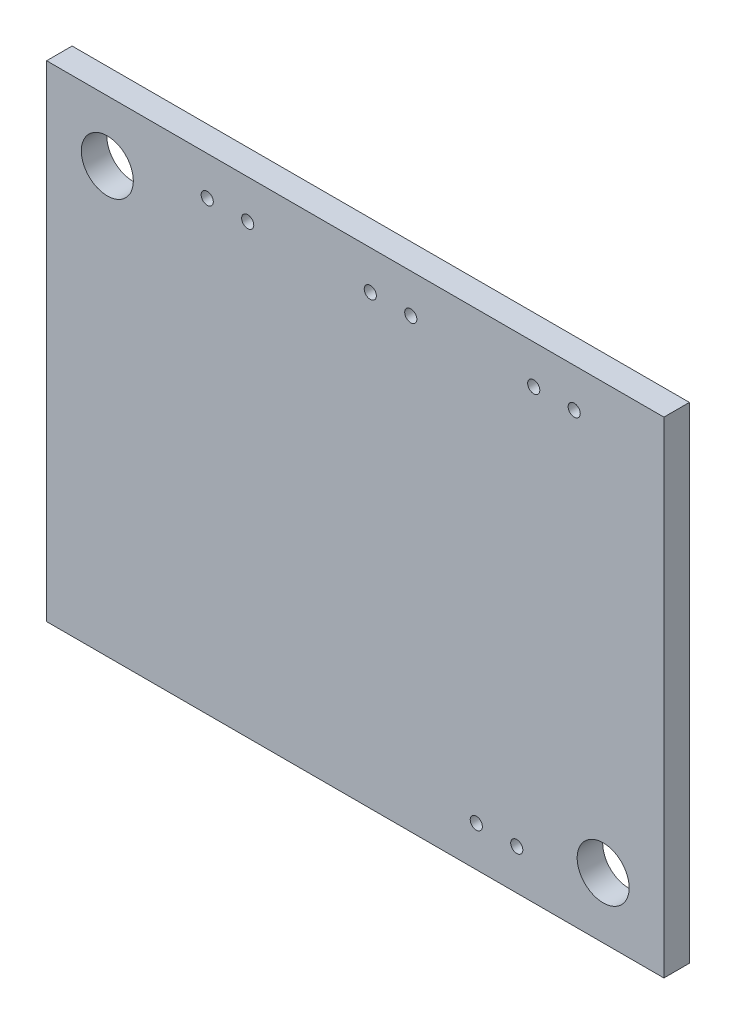
SolidWorks part; units mm, degrees
ref_plane "Front" through (0, 0, 0) normal (0, 0, 1) x (1, 0, 0)
ref_plane "Top" through (0, 0, 0) normal (0, 1, 0) x (1, 0, 0)
ref_plane "Right" through (0, 0, 0) normal (1, 0, 0) x (0, 0, -1)
sketch "Sketch1" plane through (0, 0, 0) normal (0, 0, 1) x (1, 0, 0)
  line L1 (-19.3675, -15.24) -> (19.3675, -15.24)
  line L2 (-19.3675, -15.24) -> (-19.3675, 15.24)
  line L3 (-19.3675, 15.24) -> (19.3675, 15.24)
  line L4 (19.3675, -15.24) -> (19.3675, 15.24)
  line L5 (-19.3675, -15.24) -> (19.3675, 15.24) construction
  line L6 (-19.3675, 15.24) -> (19.3675, -15.24) construction
  point P0 (0, 0)
  dimension "D1" = 38.735
  dimension "D2" = 30.48
extrude "Boss-Extrude1" add sketch "Sketch1" along normal mid plane 1.6
hole_wizard "#4 Clearance Hole1" positions "Sketch3" profile "Sketch2" hole size "#4" standard "Ansi Inch"
sketch "Sketch3" plane through (0, 0, 0.8) normal (0, 0, 1) x (1, 0, 0)
  line L0 (-19.3675, 15.24) -> (-19.3675, -15.24) construction
  line L1 (-19.3675, -15.24) -> (19.3675, -15.24) construction
  point P0 (-15.5575, 11.43)
  point P1 (15.5575, -11.43)
  dimension "D1" = 3.81
  dimension "D2" = 3.81
  dimension "D3" = 34.925
  dimension "D4" = 26.67
sketch "Sketch2" plane through (-15.5575, 11.43, 0.8) normal (1, 0, 0) x (0, -1, 0)
  line L0 (0, 0) -> (0, 11.9026)
  line L1 (0, 11.9026) -> (1.6319, 10.922)
  line L2 (1.6319, 10.922) -> (1.6319, 0)
  line L5 (1.6319, 0) -> (0, 0)
  line L10 (0, 11.9026) -> (-1.632, 10.922) construction
  line L11 (0, -6.35) -> (0, 107.95) construction
  dimension "Hole Dia." = 3.2639
  dimension "Hole Depth" = 10.922
  dimension "Drill Angle" = 118
sketch "Sketch5" plane through (0, 0, 0.8) normal (0, 0, 1) x (1, 0, 0)
  point P0 (-9.2894, 12.805)
  point P1 (-6.7494, 12.805)
  point P2 (0.9438, 12.805)
  point P3 (3.4838, 12.805)
  point P4 (11.198, 12.805)
  point P5 (13.738, 12.805)
  point P6 (10.1355, -12.7093)
  point P7 (7.5955, -12.7093)
  dimension "D1" = 2.54
  dimension "D2" = 2.54
  dimension "D3" = 2.54
  dimension "D4" = 2.54
sketch "Sketch6" plane through (0, 0, 0.8) normal (0, 0, 1) x (1, 0, 0)
  circle A0 centre (-9.2894, 12.805) radius 0.381
  circle A1 centre (-6.7494, 12.805) radius 0.381
  circle A2 centre (0.9438, 12.805) radius 0.381
  circle A3 centre (3.4838, 12.805) radius 0.381
  circle A4 centre (11.198, 12.805) radius 0.381
  circle A5 centre (13.738, 12.805) radius 0.381
  circle A6 centre (7.5955, -12.7093) radius 0.381
  circle A7 centre (10.1355, -12.7093) radius 0.381
  dimension "D1" = 0.762
extrude "Cut-Extrude1" cut sketch "Sketch6" against normal through all
